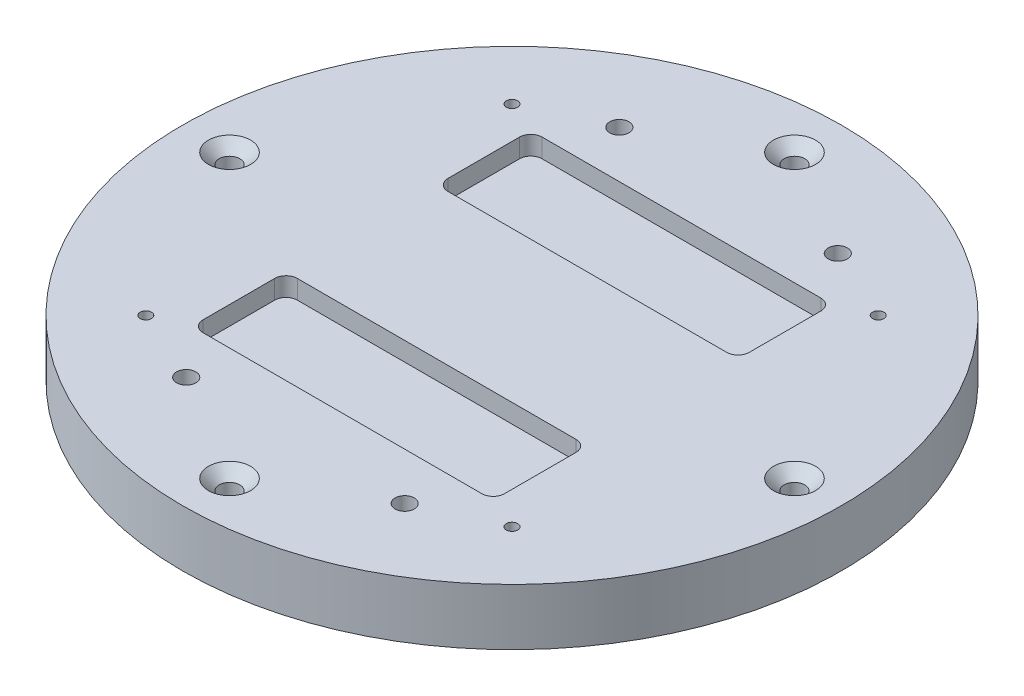
SolidWorks part; units mm, degrees
ref_plane "Front Plane" through (0, 0, 0) normal (0, 0, 1) x (1, 0, 0)
ref_plane "Top Plane" through (0, 0, 0) normal (0, 1, 0) x (1, 0, 0)
ref_plane "Right Plane" through (0, 0, 0) normal (1, 0, 0) x (0, 0, -1)
sketch "Sketch1" plane through (0, 0, 0) normal (0, 1, 0) x (1, 0, 0)
  circle A0 centre (0, 0) radius 175
  point P4 (0, 150)
  point P5 (-150, 0)
  point P6 (0, -150)
  point P7 (150, 0)
extrude "Boss-Extrude1" add sketch "Sketch1" along normal blind 30
sketch "Sketch2" plane through (0, 30, 0) normal (0, 1, 0) x (1, 0, 0)
  line L0 (0, 0) -> (-59.8535, 164.4462) construction
  line L1 (-175, 0) -> (175, 0) construction
  line L2 (0, 0) -> (0, 175) construction
  circle A0 centre (0, 0) radius 150
  circle A2 centre (0, 0) radius 175 construction
  point P3 (0, 150)
  point P4 (-150, 0)
  point P5 (0, -150)
  point P6 (150, 0)
  dimension "D1" = 90
  dimension "D6" = 300
  dimension "D2" = 90
  dimension "D3" = 90
  dimension "D4" = 70
  dimension "D5" = 0
hole_wizard "CSK for M10 SFHCS1" positions "Sketch4" profile "Sketch3" countersink size "M10" standard "ANSI Metric" end condition through all
sketch "Sketch4" plane through (0, 30, 0) normal (0, 1, 0) x (1, 0, 0)
  point P0 (-150, 0)
  point P3 (0, -150)
  point P6 (150, 0)
  point P9 (0, 150)
sketch "Sketch3" plane through (-150, 30, 0) normal (1, 0, 0) x (0, 0, 1)
  line L0 (0, 0) -> (0, 30)
  line L1 (0, 30) -> (5.5, 30)
  line L2 (5.5, 30) -> (5.5, 5.7)
  line L3 (5.5, 5.7) -> (11.2, 0)
  line L5 (11.2, 0) -> (0, 0)
  line L6 (-5.5, 5.7) -> (-11.2, 0) construction
  line L11 (0, -6.35) -> (0, 107.95) construction
  dimension "Thru Hole Dia." = 11
  dimension "Thru Hole Depth" = 30
  dimension "Near C'Sink Dia." = 22.4
  dimension "Near C'Sink Angle" = 90
sketch "Sketch5" plane through (0, 30, 0) normal (0, 1, 0) x (1, 0, 0)
  line L0 (-80, -64.99) -> (80, -64.99)
  line L1 (-80, -80) -> (80, -80)
  line L2 (-80, -80) -> (-80, 80)
  line L3 (-80, 80) -> (80, 80)
  line L4 (80, -80) -> (80, 80)
  line L5 (-80, -80) -> (80, 80) construction
  line L6 (-80, 80) -> (80, -80) construction
  line L7 (-80, 64.99) -> (80, 64.99)
  point P0 (0, 0)
  dimension "D1" = 160
  dimension "D2" = 160
  dimension "D3" = 15.01
  dimension "D4" = 15.01
sketch "Sketch6" plane through (0, 30, 0) normal (0, 1, 0) x (1, 0, 0)
  line L0 (0, 0) -> (-175, 0) construction
  circle A0 centre (0, 0) radius 175 construction
sketch "Sketch7" plane through (0, 30, 0) normal (0, 1, 0) x (1, 0, 0)
  line L0 (0, 0) -> (0, -175) construction
  line L1 (-80, 80) -> (80, -80) construction
  circle A0 centre (0, 0) radius 175 construction
sketch "Sketch8" plane through (0, 30, 0) normal (0, 1, 0) x (1, 0, 0)
  circle A0 centre (0, 0) radius 137.5
  point P4 (-97.2272, 97.2272)
  point P5 (97.2272, 97.2272)
  point P7 (-97.2272, -97.2272)
  point P8 (97.2272, -97.2272)
hole_wizard "Ø6.0mm Dowel Hole1" positions "Sketch10" profile "Sketch11" hole size "Ø6.0" standard "ANSI Metric" end condition through all
sketch "Sketch10" plane through (0, 30, 0) normal (0, 1, 0) x (1, 0, 0)
  point P0 (-97.2272, -97.2272)
  point P3 (97.2272, -97.2272)
  point P6 (97.2272, 97.2272)
  point P9 (-97.2272, 97.2272)
sketch "Sketch11" plane through (-97.2272, 30, 97.2272) normal (1, 0, 0) x (0, 0, 1)
  line L0 (0, 0) -> (0, 30)
  line L1 (0, 30) -> (3, 30)
  line L2 (3, 30) -> (3, 0)
  line L5 (3, 0) -> (0, 0)
  line L11 (0, -6.35) -> (0, 107.95) construction
  dimension "Thru Hole Dia." = 6
  dimension "Thru Hole Depth" = 30
sketch "Sketch12" plane through (0, 30, 0) normal (0, 1, 0) x (1, 0, 0)
  line L1 (-75.3032, 63.99) -> (77.0211, 63.99)
  line L2 (-75.3032, 63.99) -> (-75.3032, 48.99)
  line L3 (-75.3032, 48.99) -> (77.0211, 48.99)
  line L4 (77.0211, 63.99) -> (77.0211, 48.99)
sketch "Sketch14" plane through (0, 30, 0) normal (0, 1, 0) x (1, 0, 0)
  line L0 (-80, -80) -> (-80, 80) construction
  line L1 (-74, -40) -> (74, -40)
  line L2 (-80, -46) -> (-80, -84)
  line L3 (-74, -90) -> (74, -90)
  line L4 (80, -46) -> (80, -84)
  line L5 (80, -80) -> (80, 80) construction
  line L6 (0, 0) -> (-175, 0) construction
  line L7 (-175, 0) -> (175, 0) construction
  line L8 (80, 46) -> (80, 84)
  line L9 (-74, 40) -> (74, 40)
  line L10 (-74, 90) -> (74, 90)
  line L11 (-80, 46) -> (-80, 84)
  circle A0 centre (0, 0) radius 175 construction
  arc A1 (80, -84) -> (74, -90) centre (74, -84) cw
  arc A2 (80, -46) -> (74, -40) centre (74, -46) ccw
  arc A3 (-74, -40) -> (-80, -46) centre (-74, -46) ccw
  arc A4 (-74, -90) -> (-80, -84) centre (-74, -84) cw
  arc A5 (80, 84) -> (74, 90) centre (74, 84) ccw
  arc A6 (80, 46) -> (74, 40) centre (74, 46) cw
  arc A7 (-74, 40) -> (-80, 46) centre (-74, 46) cw
  arc A8 (-74, 90) -> (-80, 84) centre (-74, 84) ccw
  point P26 (80, -90)
  point P29 (80, -40)
  point P32 (-80, -40)
  point P35 (-80, -90)
  point P38 (80, 90)
  point P41 (80, 40)
  point P44 (-80, 40)
  point P47 (-80, 90)
  dimension "D4" = 6
  dimension "D5" = 6
  dimension "D1" = 0
  dimension "D2" = 50
  dimension "D3" = 40
extrude "Cut-Extrude2" cut sketch "Sketch14" against normal blind 10
sketch "Sketch18" plane through (0, 30, 0) normal (0, 1, 0) x (1, 0, 0)
  line L0 (58, -130) -> (58, -100) construction
  point P0 (-58, 115)
  point P1 (58, 115)
  point P3 (-58, -115)
  point P5 (58, -115)
hole_wizard "Tap Drill for M12x1.75 Tap1" positions "Sketch20" profile "Sketch21" hole size "M12x1.75" standard "ANSI Metric" end condition through all
sketch "Sketch20" plane through (0, 30, 0) normal (0, 1, 0) x (1, 0, 0)
  point P0 (-58, 115)
  point P3 (58, 115)
  point P6 (58, -115)
  point P9 (-58, -115)
sketch "Sketch21" plane through (-58, 30, -115) normal (1, 0, 0) x (0, 0, 1)
  line L0 (0, 0) -> (0, 30)
  line L1 (0, 30) -> (12.5, 30)
  line L2 (5.1, 19.4317) -> (5.1, 0)
  line L5 (5.1, 0) -> (0, 0)
  line L7 (12.5, 30) -> (5.1, 19.4317)
  line L8 (-12.5, 30) -> (-5.1, 19.4317) construction
  line L11 (0, -6.35) -> (0, 107.95) construction
  dimension "Thru Hole Dia." = 10.2
  dimension "Thru Hole Depth" = 30
  dimension "Far C'Sink Dia." = 25
  dimension "Far C'Sink Angle" = 70
